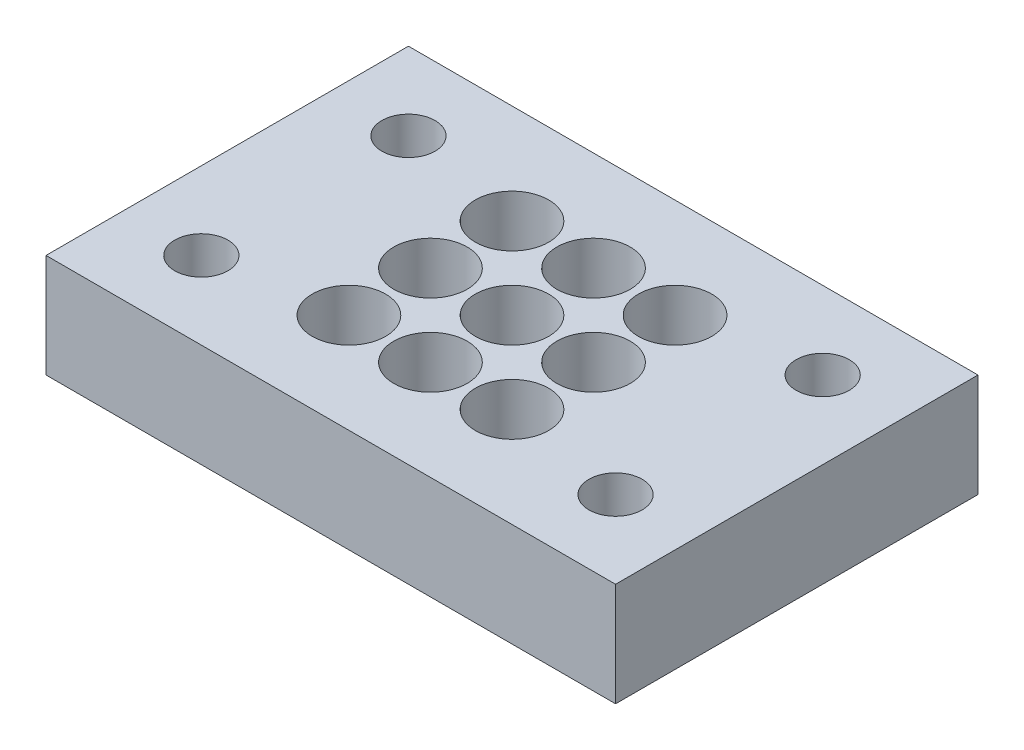
SolidWorks part; units mm, degrees
ref_plane "Front Plane" through (0, 0, 0) normal (0, 0, 1) x (1, 0, 0)
ref_plane "Top Plane" through (0, 0, 0) normal (0, 1, 0) x (1, 0, 0)
ref_plane "Right Plane" through (0, 0, 0) normal (1, 0, 0) x (0, 0, -1)
sketch "Sketch1" plane through (0, 0, 0) normal (0, 1, 0) x (1, 0, 0)
  line L0 (9.525, 34.925) -> (0, 34.925) construction
  line L1 (0, 0) -> (69.85, 0)
  line L2 (0, 0) -> (0, 44.45)
  line L3 (0, 44.45) -> (69.85, 44.45)
  line L4 (69.85, 0) -> (69.85, 44.45)
  line L5 (9.525, 34.925) -> (60.325, 34.925) construction
  line L6 (9.525, 34.925) -> (9.525, 9.525) construction
  line L7 (9.525, 9.525) -> (60.325, 9.525) construction
  line L8 (60.325, 34.925) -> (60.325, 9.525) construction
  line L9 (9.525, 34.925) -> (9.525, 44.45) construction
  circle A0 centre (9.525, 34.925) radius 3.2639
  circle A1 centre (60.325, 34.925) radius 3.2639
  circle A2 centre (9.525, 9.525) radius 3.2639
  circle A3 centre (60.325, 9.525) radius 3.2639
  circle A4 centre (34.925, 22.225) radius 4.5
  circle A5 centre (44.925, 22.225) radius 4.5
  circle A6 centre (44.925, 32.225) radius 4.5
  circle A7 centre (34.925, 32.225) radius 4.5
  circle A8 centre (24.925, 22.225) radius 4.5
  circle A9 centre (24.925, 32.225) radius 4.5
  circle A10 centre (34.925, 32.225) radius 4.5
  circle A11 centre (44.925, 22.225) radius 4.5
  circle A12 centre (44.925, 12.225) radius 4.5
  circle A13 centre (34.925, 12.225) radius 4.5
  circle A14 centre (24.925, 22.225) radius 4.5
  circle A15 centre (24.925, 12.225) radius 4.5
  circle A16 centre (34.925, 12.225) radius 4.5
  point P13 (34.925, 34.925)
  point P14 (34.925, 44.45)
  point P20 (69.85, 22.225)
  dimension "D5" = 6.5278
  dimension "D6" = 9
  dimension "D1" = 69.85
  dimension "D2" = 44.45
  dimension "D3" = 50.8
  dimension "D4" = 25.4
  dimension "D15" = 10
  dimension "D16" = 10
  dimension "D17" = 10
  dimension "D18" = 10
  dimension "D19" = 10
  dimension "D20" = 10
  dimension "D21" = 10
  dimension "D22" = 10
  dimension "D7" = 2
  dimension "D8" = 2
  dimension "D9" = 2
  dimension "D10" = 2
  dimension "D11" = 2
  dimension "D12" = 2
  dimension "D13" = 2
  dimension "D14" = 2
extrude "Boss-Extrude1" add sketch "Sketch1" along normal blind 12.7 contours L1 L4 L3 L2 A15 A13 A12 A9 A8 A7 A6 A5 A4 A3 A2 A1 A0
equation "\"o\"= 10mm"
equation "\"P\"= 10"
